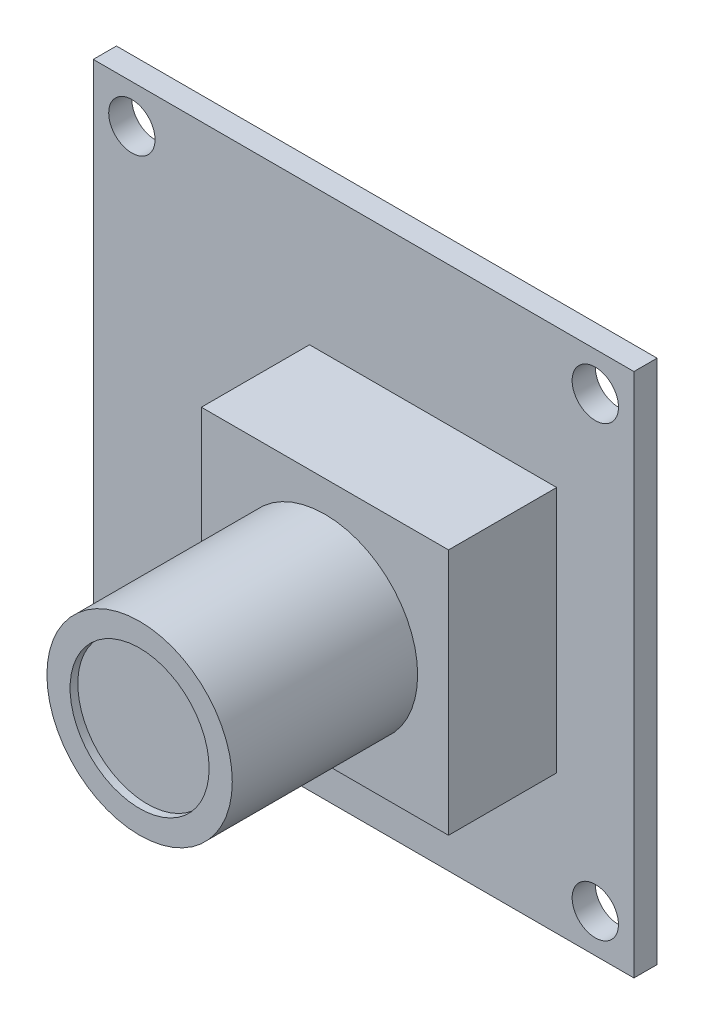
SolidWorks part; units mm, degrees
ref_plane "Front Plane" through (0, 0, 0) normal (0, 0, 1) x (1, 0, 0)
ref_plane "Top Plane" through (0, 0, 0) normal (0, 1, 0) x (1, 0, 0)
ref_plane "Right Plane" through (0, 0, 0) normal (1, 0, 0) x (0, 0, -1)
sketch "Sketch1" plane through (0, 0, 0) normal (0, 0, 1) x (1, 0, 0)
  line L1 (-17.5, 17) -> (17.5, 17)
  line L2 (-17.5, 17) -> (-17.5, -17)
  line L3 (-17.5, -17) -> (17.5, -17)
  line L4 (17.5, 17) -> (17.5, -17)
  line L5 (-17.5, 17) -> (17.5, -17) construction
  line L6 (-17.5, -17) -> (17.5, 17) construction
  point P0 (0, 0)
  dimension "D1" = 34
  dimension "D2" = 35
extrude "Boss-Extrude1" add sketch "Sketch1" against normal blind 1.5 contours L4 L3 L2 L1
sketch "Sketch2" plane through (0, 0, 0) normal (0, 0, 1) x (1, 0, 0)
  line L0 (-17.5, -17) -> (17.5, -17) construction
  line L2 (-17.5, 17) -> (-17.5, -17) construction
  line L3 (0, -11.275) -> (0, 11.275) construction
  line L4 (11.275, 0) -> (-11.275, 0) construction
  circle A0 centre (-15, -14.5) radius 1.5
  circle A1 centre (15, -14.5) radius 1.5
  circle A2 centre (15, 14.5) radius 1.5
  circle A3 centre (-15, 14.5) radius 1.5
  dimension "D1" = 3
  dimension "D2" = 2.5
  dimension "D3" = 2.5
extrude "Cut-Extrude1" cut sketch "Sketch2" against normal up to next
sketch "Sketch3" plane through (0, 0, 0) normal (0, 0, 1) x (1, 0, 0)
  line L0 (-3.5, 8) -> (12.5, 8)
  line L1 (12.5, 8) -> (12.5, -8)
  line L2 (12.5, -8) -> (-3.5, -8)
  line L3 (-3.5, -8) -> (-3.5, 8)
  line L4 (17.5, 17) -> (17.5, -17) construction
  line L5 (-17.5, 17) -> (17.5, 17) construction
  dimension "D1" = 16
  dimension "D2" = 16
  dimension "D3" = 5
  dimension "D4" = 9
extrude "Boss-Extrude3" add sketch "Sketch3" along normal blind 7
ref_plane "Plane1" through (0, 0, 7) normal (0, 0, 1) x (1, 0, 0)
sketch "Sketch4" plane through (0, 0, 7) normal (0, 0, 1) x (1, 0, 0)
  line L0 (-3.5, 0) -> (12.5, 0) construction
  line L1 (-3.5, 8) -> (-3.5, -8) construction
  line L2 (12.5, -8) -> (12.5, 8) construction
  line L3 (4.5, 8) -> (4.5, -8) construction
  line L4 (12.5, 8) -> (-3.5, 8) construction
  line L5 (-3.5, -8) -> (12.5, -8) construction
  circle A0 centre (4.5, 0) radius 6
  dimension "D1" = 12
extrude "Boss-Extrude4" add sketch "Sketch4" along normal blind 12
ref_plane "Plane2" through (0, 0, 19) normal (0, 0, 1) x (1, 0, 0)
sketch "Sketch5" plane through (0, 0, 19) normal (0, 0, 1) x (1, 0, 0)
  point P0 (4.5, 0)
sketch "Sketch6" plane through (0, 0, 0) normal (0, 0, 1) x (1, 0, 0)
  point P0 (4.5, 0)
sketch3d "3DSketch2"
  line L0 (4.5, 0, 19) -> (4.5, 0, -49981) construction
ref_plane "Plane3" through (0, 0, 19) normal (0, 0, 1) x (1, 0, 0)
sketch "Sketch7" plane through (0, 0, 19) normal (0, 0, 1) x (1, 0, 0)
  circle A0 centre (4.5, 0) radius 4.5
  dimension "D1" = 9
extrude "Cut-Extrude2" cut sketch "Sketch7" against normal blind 0.5 contours A0
ref_plane "Plane4" through (0, 0, -1.5) normal (0, 0, -1) x (-1, 0, 0)
sketch "Sketch8" plane through (0, 0, -1.5) normal (0, 0, -1) x (-1, 0, 0)
  line L1 (8, 10) -> (12, 10)
  line L2 (8, 10) -> (8, -10)
  line L3 (8, -10) -> (12, -10)
  line L4 (12, 10) -> (12, -10)
  line L5 (8, 10) -> (12, -10) construction
  line L6 (8, -10) -> (12, 10) construction
  point P0 (10, 0)
  dimension "D1" = 10
  dimension "D2" = 20
  dimension "D3" = 4
extrude "Boss-Extrude5" add sketch "Sketch8" along normal blind 6
